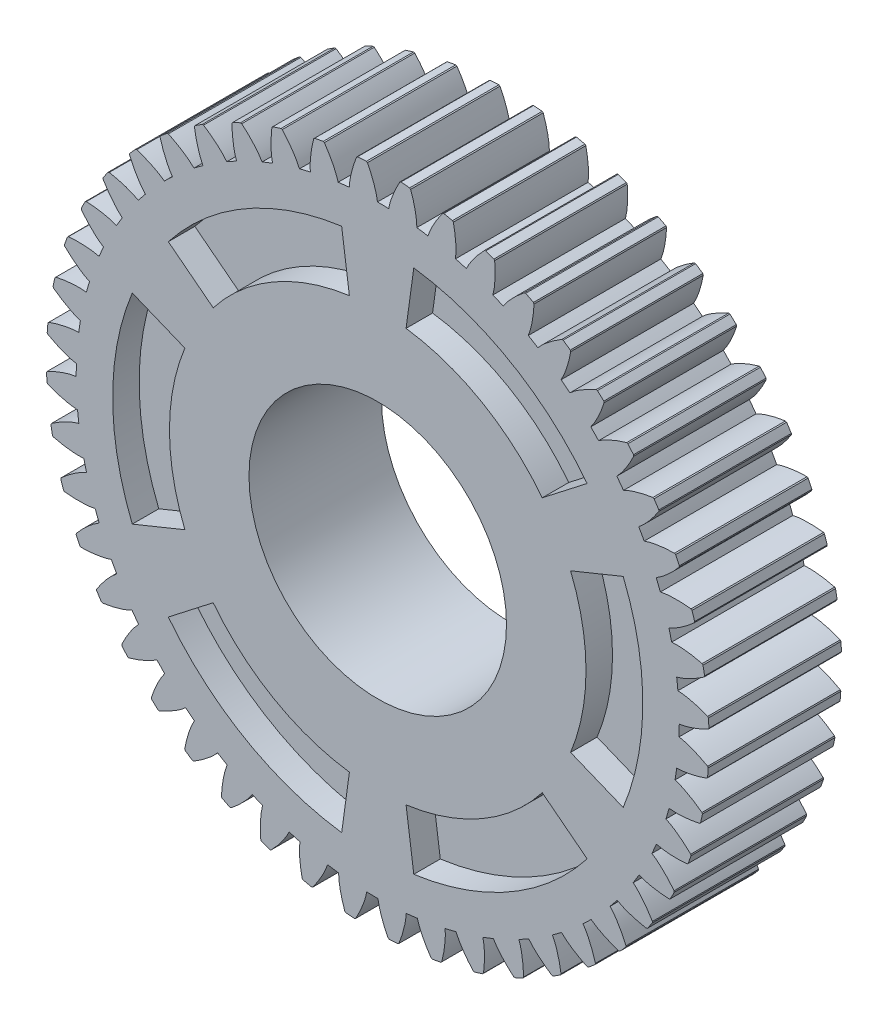
SolidWorks part; units mm, degrees
material "1.6587 (18CrNiMo7-6)"
ref_plane "Front Plane" through (0, 0, 0) normal (0, 0, 1) x (1, 0, 0)
ref_plane "Top Plane" through (0, 0, 0) normal (0, 1, 0) x (1, 0, 0)
ref_plane "Right Plane" through (0, 0, 0) normal (1, 0, 0) x (0, 0, -1)
sketch "Sketch1" plane through (0, 0, 0) normal (0, 0, 1) x (1, 0, 0)
  circle A0 centre (0, 0) radius 84 construction
  circle A1 centre (0, 0) radius 79.625
  dimension "D1" = 168
  dimension "D2" = 4.375
extrude "Boss-Extrude1" add sketch "Sketch1" along normal blind 35
sketch "Sketch2" plane through (0, 0, 0) normal (0, 0, 1) x (1, 0, 0)
  line L0 (0, 0) -> (83.9907, 1.2519) construction
  line L1 (0, 0) -> (106.5706, 5.0797) construction
  arc A0 (79.625, 0.0612) -> (79.2698, 7.5125) centre (0, 0) ccw
  circle A1 centre (0, 0) radius 84 construction
  arc A2 (87.4547, 2.8143) -> (87.3259, 5.5166) centre (0, 0) ccw
  spline S0 degree 4 poles (78.9342, 0) (78.9519, 0.0002) (79.0014, 0.0014) (79.0949, 0.0062) (79.2475, 0.0176) (79.4418, 0.0374) (79.6928, 0.069) (79.988, 0.1139) (80.312, 0.1715) (80.664, 0.2428) (81.0146, 0.3216) (81.3637, 0.4075) (81.7109, 0.4995) (82.1308, 0.6186) (82.6332, 0.772) (83.2187, 0.9668) (83.8807, 1.206) (84.5527, 1.4692) (85.2119, 1.7442) (85.8752, 2.0403) (86.515, 2.3398) (87.1766, 2.6696) (87.7857, 2.9835) (88.4645, 3.3559) (89.0113, 3.6624) (89.7285, 4.0886) (90.1509, 4.3469) (90.6436, 4.6566) (90.8617, 4.7982) (90.996, 4.8853) knots 0 0 0 0 0 0.005377 0.015084 0.028532 0.04661 0.064855 0.092111 0.119476 0.146842 0.174209 0.201575 0.228941 0.256307 0.307035 0.361767 0.4165 0.471232 0.525964 0.580697 0.635429 0.690161 0.744894 0.799626 0.854358 0.909091 0.954545 1 1 1 1 1 construction
  spline S1 degree 4 poles (79.625, 0.0612) (79.6641, 0.0664) (79.7918, 0.0841) (80.0081, 0.1175) (80.312, 0.1715) (80.664, 0.2428) (81.0146, 0.3216) (81.3637, 0.4075) (81.7109, 0.4995) (82.1308, 0.6186) (82.6332, 0.772) (83.2187, 0.9668) (83.8807, 1.206) (84.5527, 1.4692) (85.2119, 1.7442) (85.8752, 2.0403) (86.5081, 2.3366) (86.9969, 2.58) (87.3042, 2.7364) (87.4547, 2.8143) knots 0.052832 0.052832 0.052832 0.052832 0.052832 0.064855 0.092111 0.119476 0.146842 0.174209 0.201575 0.228941 0.256307 0.307035 0.361767 0.4165 0.471232 0.525964 0.580697 0.635429 0.687804 0.687804 0.687804 0.687804 0.687804
  spline S2 degree 4 poles (79.2698, 7.5125) (79.3093, 7.511) (79.4381, 7.5056) (79.6566, 7.4929) (79.9642, 7.4681) (80.3214, 7.4306) (80.6779, 7.3855) (81.0336, 7.3332) (81.388, 7.2746) (81.8173, 7.196) (82.332, 7.0911) (82.9334, 6.9528) (83.6151, 6.7777) (84.3091, 6.5796) (84.9915, 6.3686) (85.6799, 6.1369) (86.3382, 5.9022) (86.8479, 5.7063) (87.1687, 5.5798) (87.3259, 5.5166) knots 0.052832 0.052832 0.052832 0.052832 0.052832 0.064855 0.092111 0.119476 0.146842 0.174209 0.201575 0.228941 0.256307 0.307035 0.361767 0.4165 0.471232 0.525964 0.580697 0.635429 0.687804 0.687804 0.687804 0.687804 0.687804
  dimension "D1" = 159.25
  dimension "D2" = 168
  dimension "D3" = 175
  dimension "D4" = 1.875
extrude "Boss-Extrude2" add sketch "Sketch2" along normal blind 35
chamfer "Chamfer1" distance 0.2 2 edges at (87.4547, 2.8143, 17.5) (87.3259, 5.5166, 17.5)
pattern_circular "CirPattern1" count 48 over 360 about axis through (0, 0, 35) along (0, 0, -1) of "Chamfer1", "Boss-Extrude2"
sketch "Sketch3" plane through (0, 0, 35) normal (0, 0, 1) x (1, 0, 0)
  circle A0 centre (0, 0) radius 34
  dimension "D1" = 68
extrude "Cut-Extrude1" cut sketch "Sketch3" against normal blind 35
sketch "Sketch4" plane through (0, 0, 35) normal (0, 0, 1) x (1, 0, 0)
  line L0 (0, 0) -> (10.3276, 75.2273)
  line L1 (0, 0) -> (-10.3143, 75.1305)
  line L2 (0, 0) -> (0, 98.2479) construction
  line L3 (0, 0) -> (70.3125, 28.6696)
  line L4 (0, 0) -> (59.9078, 46.4977)
  line L5 (0, 0) -> (59.9849, -46.5576)
  line L6 (0, 0) -> (70.2221, -28.6328)
  line L7 (0, 0) -> (-10.3276, -75.2273)
  line L8 (0, 0) -> (10.3143, -75.1305)
  line L9 (0, 0) -> (-70.3125, -28.6696)
  line L10 (0, 0) -> (-59.9078, -46.4977)
  line L11 (0, 0) -> (-59.9849, 46.5576)
  line L12 (0, 0) -> (-70.2221, 28.6328)
  circle A0 centre (0, 0) radius 55
  circle A1 centre (0, 0) radius 70
  point P21 (0, 0)
  dimension "D1" = 15
  dimension "D2" = 110
  dimension "D3" = 15.634
  dimension "D4" = 6
extrude "Cut-Extrude3" cut sketch "Sketch4" against normal blind 7 contours L1 A1 L11 A0 | L4 A1 L0 A0 | L6 A1 L3 A0 | L8 A1 L5 A0 | L10 A1 L7 A0 | L12 A1 L9 A0
